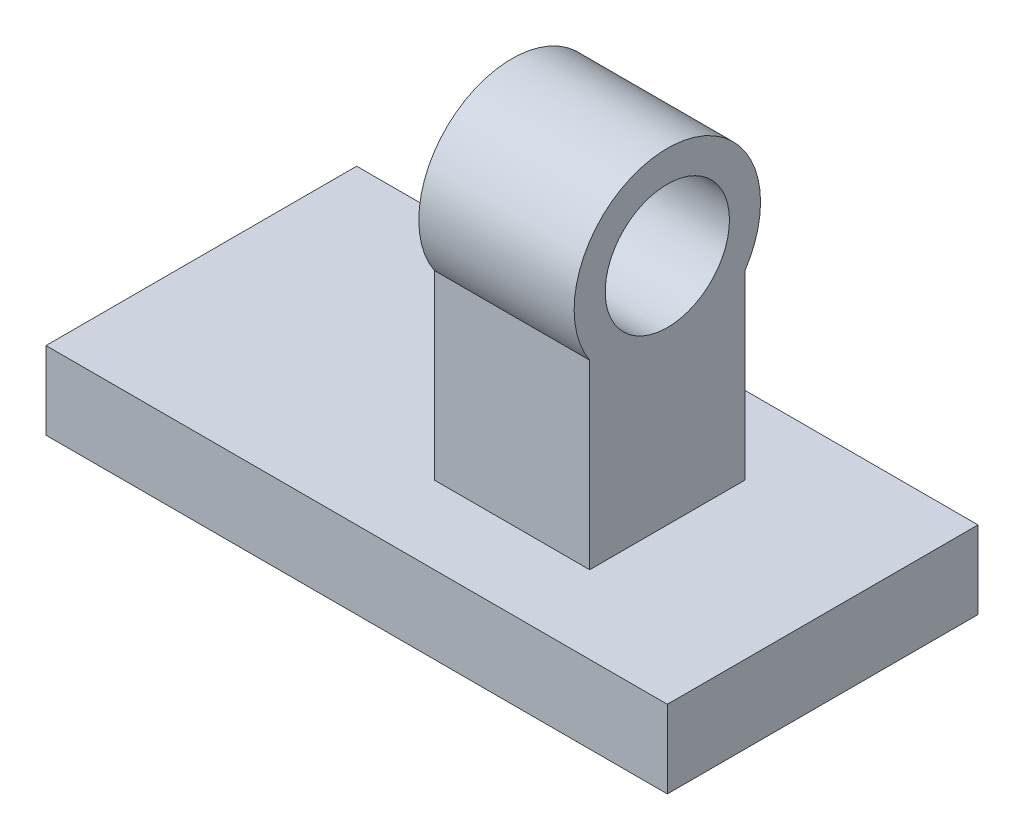
SolidWorks part; units mm, degrees
material "Pure Lead"
ref_plane "Front Plane" through (0, 0, 0) normal (0, 0, 1) x (1, 0, 0)
ref_plane "Top Plane" through (0, 0, 0) normal (0, 1, 0) x (1, 0, 0)
ref_plane "Right Plane" through (0, 0, 0) normal (1, 0, 0) x (0, 0, -1)
sketch "LinkFrame" plane through (0, 0, 0) normal (1, 0, 0) x (0, 0, -1)
  line L5 (316.7465, -249.2098) -> (316.7465, -366.0436)
  line L7 (216.7465, -249.2098) -> (216.7465, -366.0436)
  line L8 (266.7465, -216.0436) -> (266.7465, -416.0436) construction
  line L9 (166.7465, -366.0436) -> (216.7465, -366.0436)
  line L10 (166.7465, -366.0436) -> (166.7465, -416.0436)
  line L11 (166.7465, -416.0436) -> (366.7465, -416.0436)
  line L12 (366.7465, -366.0436) -> (366.7465, -416.0436)
  line L13 (316.7465, -366.0436) -> (366.7465, -366.0436)
  line L14 (226.7933, -214.1094) -> (266.7465, -216.0436) construction
  circle A6 centre (266.7465, -216.0436) radius 40
  arc A7 (316.7465, -249.2098) -> (216.7465, -249.2098) centre (266.7465, -216.0436) ccw
  dimension "D6" = 80
  dimension "D2" = 120
  dimension "D10" = 50
  dimension "D9" = 50
  dimension "D12" = 50
  dimension "D11" = 200
  dimension "D3" = 200
extrude "Boss-Extrude1" add sketch "LinkFrame" along normal blind 100
sketch "ExtendedPress" plane through (0, 0, 0) normal (1, 0, 0) x (0, 0, -1)
  line L1 (366.7465, -366.0436) -> (166.7465, -366.0436)
  line L2 (366.7465, -366.0436) -> (366.7465, -416.0436)
  line L3 (366.7465, -416.0436) -> (166.7465, -416.0436)
  line L4 (166.7465, -366.0436) -> (166.7465, -416.0436)
extrude "Boss-Extrude2" add sketch "ExtendedPress" along normal mid plane 400 contours L2 L1 L4 L3
equation "\"LinkLength\"= 80cm"
equation "\"D6@LinkFrame\"=\"HoleMountDiameter@PrintingPress.Assembly\""
equation "\"D1@Boss-Extrude1\"=\"RivetLength@PrintingPress.Assembly\""
equation "\"D10@LinkFrame\"=0.5*\"RivetLength@PrintingPress.Assembly\""
equation "\"D9@LinkFrame\"=0.5*\"RivetLength@PrintingPress.Assembly\""
equation "\"D12@LinkFrame\"=0.5*\"RivetLength@PrintingPress.Assembly\""
equation "\"D2@LinkFrame\"=1.5*\"HoleMountDiameter@PrintingPress.Assembly\""
equation "\"D3@LinkFrame\"=2.0*\"RivetLength@PrintingPress.Assembly\""
equation "\"D1@Boss-Extrude2\"=4*\"RivetLength@PrintingPress.Assembly\""
